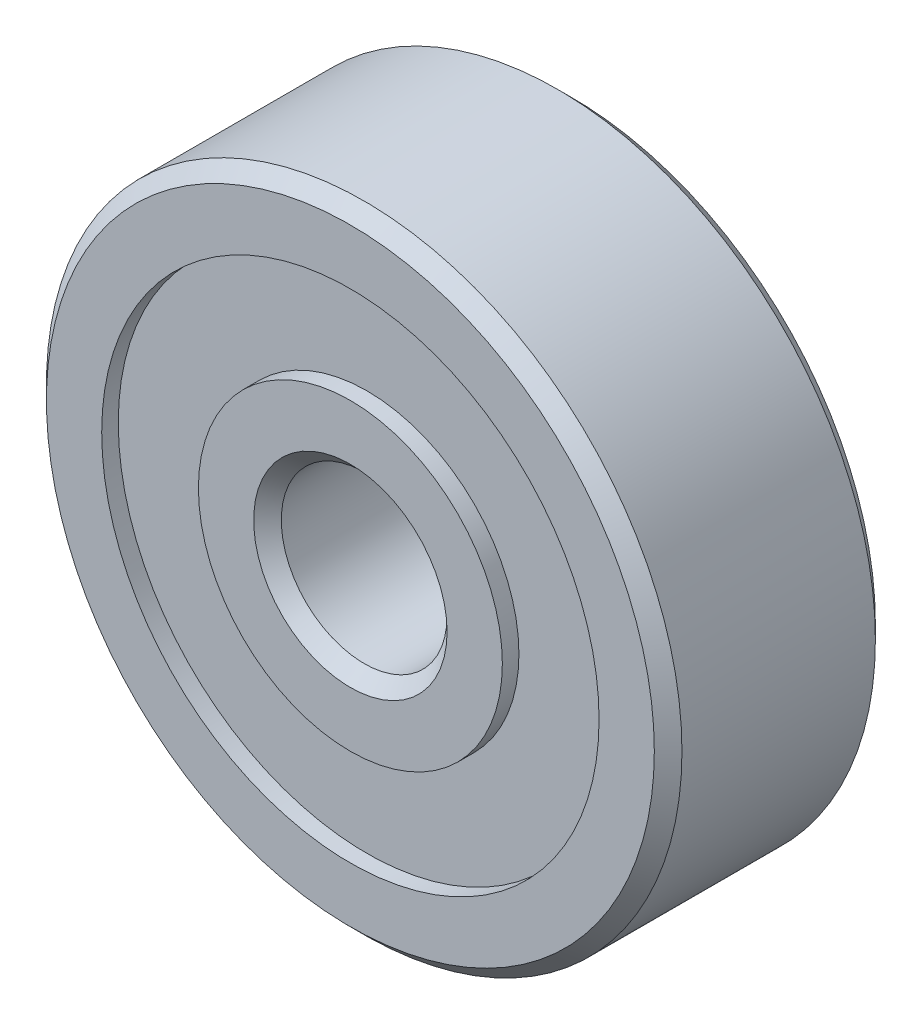
SolidWorks part; units mm, degrees
ref_plane "Front Plane" through (0, 0, 0) normal (0, 0, 1) x (1, 0, 0)
ref_plane "Top Plane" through (0, 0, 0) normal (0, 1, 0) x (1, 0, 0)
ref_plane "Right Plane" through (0, 0, 0) normal (1, 0, 0) x (0, 0, -1)
sketch "Sketch1" plane through (0, 0, 0) normal (0, 0, 1) x (1, 0, 0)
  circle A0 centre (0, 0) radius 5.75
  circle A1 centre (0, 0) radius 1.5
  dimension "D1" = 3
  dimension "D2" = 11.5
extrude "Boss-Extrude1" add sketch "Sketch1" along normal mid plane 4
chamfer "Chamfer1" distance 0.25 angle 45 4 edges at (1.5, 0, -2) (1.5, 0, 2) (5.75, 0, -2) (5.75, 0, 2)
sketch "Sketch2" plane through (0, 0, 0) normal (0, 1, 0) x (1, 0, 0)
  line L0 (-5.5, -2) -> (5.5, -2) construction
  line L1 (-4.5, -2) -> (-2.75, -2)
  line L2 (-4.5, -2) -> (-4.5, -1.7)
  line L3 (-4.5, -1.7) -> (-2.75, -1.7)
  line L4 (-2.75, -2) -> (-2.75, -1.7)
  line L5 (0, 0) -> (0, 3.701) construction
  dimension "D1" = 1
  dimension "D2" = 1
  dimension "D3" = 0.3
revolve "Cut-Revolve1" cut sketch "Sketch2" angle 360 about L5
mirror "Mirror1" about plane through (0, 0, 0) normal (0, 0, 1) of "Cut-Revolve1"
